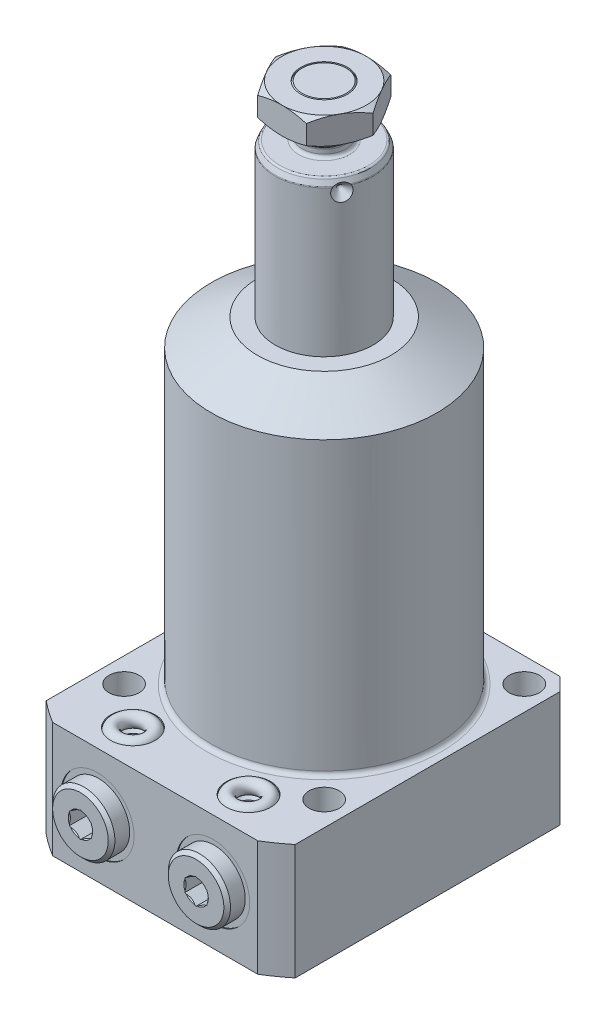
SolidWorks part; units mm, degrees
material "AISI 1020"
ref_plane "Front Plane" through (0, 0, 0) normal (0, 0, 1) x (1, 0, 0)
ref_plane "Top Plane" through (0, 0, 0) normal (0, 1, 0) x (1, 0, 0)
ref_plane "Right Plane" through (0, 0, 0) normal (1, 0, 0) x (0, 0, -1)
sketch "Sketch1" plane through (0, 0, 0) normal (0, 0, 1) x (1, 0, 0)
  line L0 (11, 0) -> (11, 104.5)
  line L1 (11, 104.5) -> (10.3005, 106)
  line L2 (10.3005, 106) -> (5, 106)
  line L3 (5, 106) -> (5, 108)
  line L4 (5, 108) -> (5.935, 108.935)
  line L5 (5.935, 108.935) -> (5.935, 116.5)
  line L6 (5.935, 116.5) -> (4.935, 117.5)
  line L7 (4.935, 117.5) -> (0, 117.5)
  line L8 (0, -3.075) -> (0, 64.575) construction
  line L9 (11, 0) -> (0, 0)
  line L10 (0, 0) -> (0, 117.5)
  line L11 (-18.7015, -26) -> (46.2776, -26) construction
  dimension "D1" = 11.5
  dimension "D2" = 22
  dimension "D3" = 10
  dimension "D4" = 11.87
  dimension "D5" = 143.5
  dimension "D6" = 25
  dimension "D7" = 1.5
  dimension "D8" = 45
  dimension "D9" = 1
  dimension "D10" = 8.565
  dimension "D11" = 4.935
  dimension "D12" = 26
revolve "Revolve2" add sketch "Sketch1" angle 360 about L8
fillet "Fillet2" radius 0.75 2 edges at (0, 106, -5) (0, 108, -5)
fillet "Fillet3" radius 0.5 2 edges at (0, 104.5, -11) (0, 106, -10.3005)
sketch "Sketch2" plane through (0, 0, 0) normal (1, 0, 0) x (0, 0, -1)
  line L0 (9, 103.33) -> (11, 101.33)
  line L1 (4.2016, 103.33) -> (7.575, 103.33) construction
  line L2 (9.982, 106) -> (-9.982, 106) construction
  line L3 (11, 101.33) -> (11, 103.33)
  line L4 (11, 103.33) -> (9, 103.33)
  line L5 (11, 0) -> (11, 104.3892) construction
  dimension "D1" = 2.67
  dimension "D2" = 45
  dimension "D3" = 4
revolve "Cut-Revolve1" cut sketch "Sketch2" angle 360 about L1
sketch "Sketch3" plane through (0, 117.5, 0) normal (0, 1, 0) x (1, 0, 0)
  line L1 (10.9697, 0) -> (5.4848, 9.5)
  line L2 (5.4848, 9.5) -> (-5.4848, 9.5)
  line L3 (-5.4848, 9.5) -> (-10.9697, 0)
  line L4 (-10.9697, 0) -> (-5.4848, -9.5)
  line L5 (-5.4848, -9.5) -> (5.4848, -9.5)
  line L6 (5.4848, -9.5) -> (10.9697, 0)
  circle A0 centre (0, 0) radius 9.5 construction
  circle A1 centre (0, 0) radius 5.25
  dimension "D2" = 10.5
  dimension "D1" = 19
extrude "Extrude3" add sketch "Sketch3" against normal blind 6
pattern_circular "CirPattern1" count 3 over 360 about axis through (0, -3.075, 0) along (0, -1, 0) of "Cut-Revolve1"
sketch "Sketch4" plane through (0, 0, 0) normal (1, 0, 0) x (0, 0, -1)
  line L0 (9.5, 117.5) -> (12.5, 117.5)
  line L1 (12.5, 117.5) -> (12.5, 115.7679)
  line L2 (12.5, 115.7679) -> (9.5, 117.5)
  line L3 (9.5, 114.5) -> (-10.9636, 114.5) construction
  line L4 (9.5, 111.5) -> (9.5, 117.5) construction
  line L5 (12.5, 113.2321) -> (9.5, 111.5)
  line L6 (12.5, 111.5) -> (12.5, 113.2321)
  line L7 (9.5, 111.5) -> (12.5, 111.5)
  dimension "D1" = 30
  dimension "D2" = 3
revolve "Cut-Revolve3" cut sketch "Sketch4" angle 360 about axis through (0, -3.075, 0) along (0, -1, 0)
sketch "Sketch6" plane through (0, 0, 0) normal (0, 0, 1) x (1, 0, 0)
  line L0 (0, 0) -> (0, 71.3762) construction
  line L1 (0, 71.5) -> (15, 71.5)
  line L2 (15, 71.5) -> (25.385, 65.5042)
  line L3 (44.45, -26) -> (44.45, 0)
  line L4 (44.45, 0) -> (25.385, 0)
  line L5 (25.385, 65.5042) -> (25.385, 0)
  line L6 (44.45, -26) -> (0, -26)
  line L7 (0, -26) -> (0, 71.5)
  dimension "D1" = 50.77
  dimension "D2" = 26
  dimension "D3" = 97.5
  dimension "D4" = 88.9
  dimension "D5" = 30
  dimension "D6" = 30
revolve "Revolve3" add sketch "Sketch6" angle 360 about L0
sketch "Sketch7" plane through (0, 0, 0) normal (0, 1, 0) x (-1, 0, 0)
  line L0 (0, 0) -> (0, -52.3237) construction
  line L1 (-28, 38) -> (28, 38)
  line L2 (-28, 38) -> (-28, -28)
  line L3 (-28, -28) -> (28, -28)
  line L4 (28, 38) -> (28, -28)
  dimension "D1" = 56
  dimension "D2" = 66
  dimension "D3" = 28
extrude "Cut-Extrude5" cut sketch "Sketch7" against normal through all flip side to cut
sketch "Sketch8" plane through (0, 0, 0) normal (0, 1, 0) x (-1, 0, 0)
  circle A0 centre (-22.5, 22.5) radius 3.4
  dimension "D1" = 6.8
  dimension "D2" = 22.5
  dimension "D3" = 22.5
extrude "Cut-Extrude6" cut sketch "Sketch8" against normal through all
pattern_circular "CirPattern2" count 4 over 360 about axis through (0, 0, 0) along (0, 1, 0) of "Cut-Extrude6"
chamfer "Chamfer1" distance 3 angle 45 2 edges at (-28, -13, -28) (28, -13, -28)
fillet "Fillet5" radius 1 1 edges at (0, 0, -25.385)
ref_plane "Plane1" through (0, -13, 0) normal (0, 1, 0) x (-1, 0, 0)
sketch "Sketch11" plane through (0, -13, 0) normal (0, 1, 0) x (-1, 0, 0)
  line L0 (-13, 42.9716) -> (-13, 19.7499) construction
  line L1 (-21.25, 38) -> (-21.25, 37.75)
  line L2 (23.0608, 38) -> (-23.0608, 38) construction
  line L3 (-21.25, 37.75) -> (-18, 37.75)
  line L4 (-18, 37.75) -> (-17.42, 37.17)
  line L5 (-17.42, 37.17) -> (-17.42, 22.59)
  line L6 (-17.42, 22.59) -> (-13, 22.59)
  line L7 (-13, 22.59) -> (-13, 38)
  line L8 (-13, 38) -> (-21.25, 38)
  dimension "D1" = 13
  dimension "D2" = 0.25
  dimension "D3" = 8.84
  dimension "D4" = 15.16
  dimension "D5" = 16.5
  dimension "D6" = 45
  dimension "D7" = 0.58
revolve "Cut-Revolve5" cut sketch "Sketch11" angle 360 about L0
ref_plane "Plane2" through (0, 0, 30) normal (0, 0, 1) x (1, 0, 0)
sketch "Sketch13" plane through (0, 0, 30) normal (0, 0, 1) x (1, 0, 0)
  line L0 (-15.5, -14) -> (-15.5, -23.125)
  line L1 (-15.5, -23.125) -> (-16.125, -23.75)
  line L2 (-16.125, -23.75) -> (-18, -23.75)
  line L3 (-18, -23.75) -> (-18, -26)
  line L5 (-18, -26) -> (-13, -26)
  line L6 (-13, -26) -> (-13, -14)
  line L7 (-13, -14) -> (-15.5, -14)
  line L8 (-13, -28.8487) -> (-13, -4.3918) construction
  line L9 (23.0608, -26) -> (-23.0608, -26) construction
  dimension "D1" = 13
  dimension "D2" = 5
  dimension "D3" = 12
  dimension "D4" = 2.25
  dimension "D5" = 10
  dimension "D6" = 45
  dimension "D7" = 0.625
revolve "Cut-Revolve6" cut sketch "Sketch13" angle 360 about L8
mirror "Mirror4" about plane through (0, -13, 0) normal (0, 1, 0) of "Cut-Revolve6"
sketch "Sketch14" plane through (0, -13, 0) normal (0, 1, 0) x (-1, 0, 0)
  line L0 (-13, 32.5881) -> (-13, 43.3353) construction
  line L1 (-13, 22.59) -> (-13, 37.17) construction
  line L2 (-15.75, 41.81) -> (-19.25, 41.81)
  line L3 (-19.25, 41.81) -> (-20, 41.06)
  line L4 (-20, 41.06) -> (-20, 37.75)
  line L5 (-4.75, 37.75) -> (-21.25, 37.75) construction
  line L6 (-20, 37.75) -> (-17.125, 37.75)
  line L7 (-8, 37.75) -> (-18, 37.75) construction
  line L8 (-17.125, 37.75) -> (-17.125, 35.3078)
  line L9 (-17.125, 35.3078) -> (-13, 35.3078)
  line L10 (-13, 35.3078) -> (-13, 35.3088)
  line L11 (-13, 35.3088) -> (-15.5, 36.811)
  line L12 (-15.5, 36.811) -> (-15.5, 41.56)
  line L13 (-15.5, 41.56) -> (-15.75, 41.81)
  dimension "D1" = 8.25
  dimension "D2" = 2.4422
  dimension "D3" = 59
  dimension "D4" = 5
  dimension "D5" = 4.06
  dimension "D6" = 14
  dimension "D7" = 45
  dimension "D8" = 0.75
  dimension "D9" = 45
  dimension "D10" = 0.25
  dimension "D11" = 0.001
revolve "Revolve6" add sketch "Sketch14" angle 360 about L0
sketch "Sketch15" plane through (0, 0, 41.81) normal (0, 0, 1) x (1, 0, 0)
  line L1 (15.5, -14.4434) -> (15.5, -11.5566)
  line L2 (15.5, -11.5566) -> (13, -10.1132)
  line L3 (13, -10.1132) -> (10.5, -11.5566)
  line L4 (10.5, -11.5566) -> (10.5, -14.4434)
  line L5 (10.5, -14.4434) -> (13, -15.8868)
  line L6 (13, -15.8868) -> (15.5, -14.4434)
  circle A0 centre (13, -13) radius 2.5 construction
  dimension "D1" = 5
extrude "Cut-Extrude8" cut sketch "Sketch15" against normal blind 4.06
mirror "Mirror1" about plane through (0, 0, 0) normal (1, 0, 0) of "Mirror4", "Cut-Revolve5", "Cut-Revolve6", "Revolve6", "Cut-Extrude8"
sketch "Sketch16" plane through (0, 0, 30) normal (0, 0, 1) x (1, 0, 0)
  line L1 (-13, 9.3219) -> (-13, -15.1063) construction
  line L2 (-13, -23.125) -> (-13, -16.6451) construction
  line L3 (-23.0608, 0) -> (23.0608, 0) construction
  circle A0 centre (-16.5, -0.75) radius 1.5
  dimension "D1" = 3
  dimension "D3" = 0.75
  dimension "D2" = 7
revolve "Revolve7" add sketch "Sketch16" angle 360 about L1
mirror "Mirror3" about plane through (0, 0, 0) normal (1, 0, 0) of bodies 128
mirror "Mirror5" about plane through (0, -13, 0) normal (0, 1, 0) of bodies 128 130
